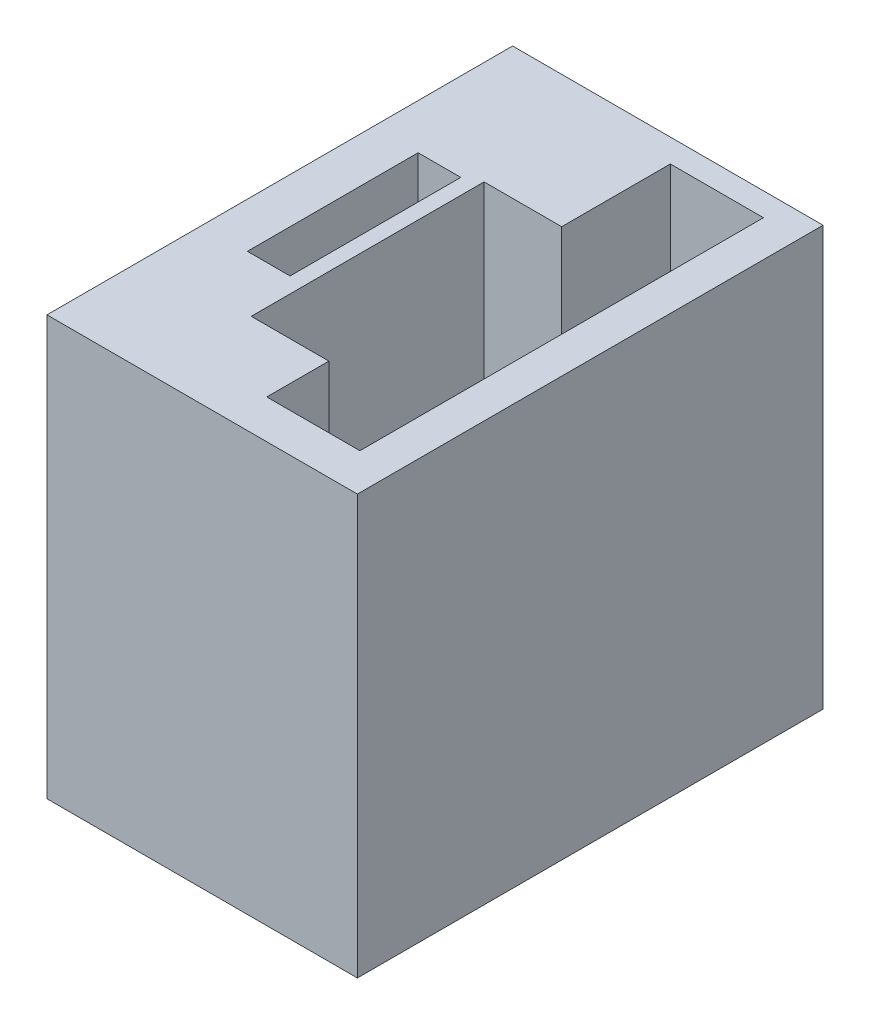
SolidWorks part; units mm, degrees
ref_plane "Front Plane" through (0, 0, 0) normal (0, 0, 1) x (1, 0, 0)
ref_plane "Top Plane" through (0, 0, 0) normal (0, 1, 0) x (1, 0, 0)
ref_plane "Right Plane" through (0, 0, 0) normal (1, 0, 0) x (0, 0, -1)
sketch "Sketch2" plane through (0, 0, 0) normal (1, 0, 0) x (0, 0, -1)
  line L1 (0, 0) -> (30, 0)
  line L2 (0, 0) -> (0, 27)
  line L3 (0, 27) -> (30, 27)
  line L4 (30, 0) -> (30, 27)
  dimension "D1" = 30
  dimension "D2" = 27
extrude "Boss-Extrude1" add sketch "Sketch2" along normal blind 20
sketch "Sketch6" plane through (2.2961, 27, -0.2935) normal (0, 1, 0) x (1, 0, 0)
  line L0 (17.7039, 29.7065) -> (-2.2961, 29.7065) construction
  line L5 (9.3658, 28.2065) -> (15.3658, 28.2065)
  line L6 (9.3658, 28.2065) -> (9.3658, 2.2065)
  line L7 (9.3658, 2.2065) -> (15.3658, 2.2065)
  line L8 (15.3658, 28.2065) -> (15.3658, 2.2065)
  dimension "D1" = 6
  dimension "D2" = 26
  dimension "D3" = 1.5
extrude "Cut-Extrude4" cut sketch "Sketch6" against normal blind 26 contours L8 L7 L6 L5
sketch "Sketch9" plane through (0, 27, 0) normal (0, 1, 0) x (1, 0, 0)
  line L0 (11.662, 28.5) -> (11.662, 2.5) construction
  line L1 (6.662, 21.5) -> (11.662, 21.5)
  line L2 (6.662, 21.5) -> (6.662, 6.5)
  line L3 (6.662, 6.5) -> (11.662, 6.5)
  line L4 (11.662, 21.5) -> (11.662, 6.5)
  line L5 (11.662, 28.5) -> (17.662, 28.5) construction
  line L6 (11.662, 2.5) -> (17.662, 2.5) construction
  dimension "D1" = 7
  dimension "D2" = 4
  dimension "D3" = 5
extrude "Cut-Extrude5" cut sketch "Sketch9" against normal blind 21
sketch "Sketch11" plane through (0, 0, 0) normal (-1, 0, 0) x (0, 0, 1)
  line L0 (-30, 27) -> (0, 27) construction
  line L1 (-30, 0) -> (-30, 27) construction
  circle A0 centre (-15.1, 13.5) radius 5
  dimension "D1" = 13.5
  dimension "D2" = 14.9
extrude "Cut-Extrude8" cut sketch "Sketch11" against normal blind 0.5
sketch "Sketch12" plane through (0, 27, 0) normal (0, 1, 0) x (1, 0, 0)
  line L0 (6.662, 21.5) -> (6.662, 6.5) construction
  line L1 (2.912, 21) -> (5.662, 21)
  line L2 (2.912, 21) -> (2.912, 10)
  line L3 (2.912, 10) -> (5.662, 10)
  line L4 (5.662, 21) -> (5.662, 10)
  line L6 (11.662, 28.5) -> (17.662, 28.5) construction
  line L7 (11.662, 2.5) -> (17.662, 2.5) construction
  point P6 (4.287, 10)
  point P9 (5.662, 15.5)
  dimension "D1" = 7.5
  dimension "D2" = 7.5
  dimension "D3" = 2.75
  dimension "D4" = 1
extrude "Cut-Extrude12" cut sketch "Sketch12" against normal blind 17.5
sketch "Sketch15" plane through (0.5, 0, 0) normal (-1, 0, 0) x (0, 0, 1)
  line L0 (-30, 0) -> (-30, 27) construction
  line L1 (-30, 27) -> (0, 27) construction
  circle A0 centre (-15.04, 13.5) radius 4.5
  dimension "D1" = 14.96
  dimension "D2" = 13.5
extrude "Cut-Extrude13" cut sketch "Sketch15" against normal blind 6
sketch "Sketch16" plane through (0, 0, 0) normal (0, 0, 1) x (1, 0, 0)
